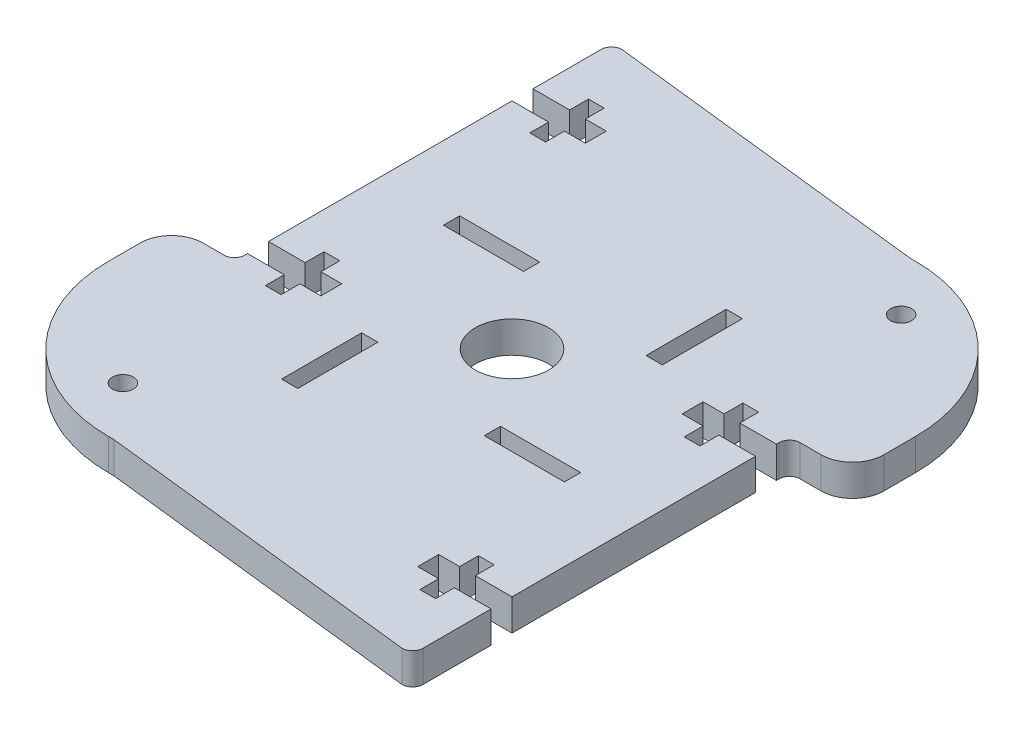
SolidWorks part; units mm, degrees
material "Acrílico (médio-alto impacto)"
ref_plane "Plano frontal" through (0, 0, 0) normal (0, 0, 1) x (1, 0, 0)
ref_plane "Plano superior" through (0, 0, 0) normal (0, 1, 0) x (1, 0, 0)
ref_plane "Plano direito" through (0, 0, 0) normal (1, 0, 0) x (0, 0, -1)
sketch "Esboço1" plane through (0, 0, 0) normal (0, 1, 0) x (1, 0, 0)
  line L1 (-26.5, -30) -> (26.5, -30)
  line L2 (-26.5, -30) -> (-26.5, 30)
  line L3 (-26.5, 30) -> (26.5, 30)
  line L4 (26.5, -30) -> (26.5, 30)
  line L5 (-26.5, -30) -> (26.5, 30) construction
  line L6 (-26.5, 30) -> (26.5, -30) construction
  point P0 (0, 0)
  dimension "D1" = 53
  dimension "D2" = 60
extrude "Ressalto-extrusão1" add sketch "Esboço1" along normal blind 3
sketch "Esboço4" plane through (0, 3, 0) normal (0, 1, 0) x (-1, 0, 0)
  line L0 (-11.5, -26.5) -> (11.5, -26.5) construction
  line L2 (-26.5, 30) -> (-26.5, -30) construction
  line B0 (-6.95, -13.5) -> (-8.5, -13.5)
  line B1 (-6.95, -13.5) -> (-6.95, -5.85)
  line B2 (-6.95, -5.85) -> (-8.5, -5.85)
  line B3 (-8.5, -13.5) -> (-8.5, -5.85)
  line B4 (-13.5, 6.95) -> (-13.5, 8.5)
  line B5 (-13.5, 6.95) -> (-5.85, 6.95)
  line B6 (-5.85, 6.95) -> (-5.85, 8.5)
  line B7 (-13.5, 8.5) -> (-5.85, 8.5)
  line B8 (6.95, 13.5) -> (8.5, 13.5)
  line B9 (6.95, 13.5) -> (6.95, 5.85)
  line B10 (6.95, 5.85) -> (8.5, 5.85)
  line B11 (8.5, 13.5) -> (8.5, 5.85)
  line B12 (13.5, -6.95) -> (13.5, -8.5)
  line B13 (13.5, -6.95) -> (5.85, -6.95)
  line B14 (5.85, -6.95) -> (5.85, -8.5)
  line B15 (13.5, -8.5) -> (5.85, -8.5)
  dimension "D1" = 18
  dimension "D2" = 13
sketch_block_instance "Bloco2-1"
sketch_block "Bloco2" parameters "D1"=7.65, "D2"=1.55
sketch_block_instance "Bloco2-5"
sketch_block_instance "Bloco2-14"
sketch_block_instance "Bloco2-15"
sketch_block_instance "Bloco2-16"
extrude "Corte-extrusão2" cut sketch "Esboço4" against normal blind 10
sketch "Esboço5" plane through (0, 3, 0) normal (0, 1, 0) x (1, 0, 0)
  circle A4 centre (-15.7426, -21.3995) radius 1
  circle A7 centre (15.7426, 21.3995) radius 1
  dimension "D4" = 2
extrude "Corte-extrusão3" cut sketch "Esboço5" against normal through all
sketch "Esboço7" plane through (0, 3, 0) normal (0, 1, 0) x (1, 0, 0)
  circle A0 centre (0, 0) radius 3.5
  dimension "D1" = 7
extrude "Corte-extrusão6" cut sketch "Esboço7" against normal through all
sketch "Esboço8" plane through (0, 3, 0) normal (0, 1, 0) x (1, 0, 0)
  line L0 (26.5, -30) -> (26.5, 30) construction
  line L1 (26.5, 6) -> (20.5, 6)
  line L2 (26.5, 6) -> (26.5, -30)
  line L3 (26.5, -30) -> (20.5, -30)
  line L4 (20.5, 6) -> (20.5, -30)
  line L5 (-26.5, -30) -> (26.5, -30) construction
  line L6 (-26.5, -6) -> (-20.5, -6)
  line L8 (-26.5, -6) -> (-26.5, 30)
  line L9 (-26.5, 30) -> (-20.5, 30)
  line L10 (-20.5, -6) -> (-20.5, 30)
  dimension "D1" = 6
  dimension "D2" = 36
  dimension "D3" = 2
extrude "Corte-extrusão7" cut sketch "Esboço8" against normal through all
fillet "Filete2" radius 3 2 edges at (-26.5, 1.5, 6) (26.5, 1.5, -6)
fillet "Filete3" radius 1 4 edges at (-20.5, 1.5, -30) (20.5, 1.5, 30) (-20.5, 1.5, 6) (20.5, 1.5, -6)
sketch "Esboço9" plane through (0, 3, 0) normal (0, 1, 0) x (1, 0, 0)
  line L0 (-20.5, -5) -> (-20.5, 29) construction
  line L1 (26.5, 30) -> (-19.5, 30) construction
  line B0 (-13.5, 20.5) -> (-15.5, 20.5)
  line B1 (-13.5, 20.5) -> (-13.5, 22.5)
  line B2 (-20.5, 20.5) -> (-20.5, 22.5)
  line B3 (-13.5, 22.5) -> (-15.5, 22.5)
  line B4 (-15.5, 18.7) -> (-15.5, 20.5)
  line B5 (-15.5, 18.7) -> (-17, 18.7)
  line B6 (-17, 18.7) -> (-17, 20.5)
  line B7 (-15.5, 24.3) -> (-17, 24.3)
  line B8 (-17, 22.5) -> (-20.5, 22.5)
  line B9 (-15.5, 22.5) -> (-15.5, 24.3)
  line B10 (-17, 22.5) -> (-17, 24.3)
  line B11 (-17, 20.5) -> (-20.5, 20.5)
  line B12 (-13.5, -4.7435) -> (-15.5, -4.7435)
  line B13 (-13.5, -4.7435) -> (-13.5, -2.7435)
  line B14 (-20.5, -4.7435) -> (-20.5, -2.7435)
  line B15 (-13.5, -2.7435) -> (-15.5, -2.7435)
  line B16 (-15.5, -6.5435) -> (-15.5, -4.7435)
  line B17 (-15.5, -6.5435) -> (-17, -6.5435)
  line B18 (-17, -6.5435) -> (-17, -4.7435)
  line B19 (-15.5, -0.9435) -> (-17, -0.9435)
  line B20 (-17, -2.7435) -> (-20.5, -2.7435)
  line B21 (-15.5, -2.7435) -> (-15.5, -0.9435)
  line B22 (-17, -2.7435) -> (-17, -0.9435)
  line B23 (-17, -4.7435) -> (-20.5, -4.7435)
  line B24 (13.5, -20.5) -> (15.5, -20.5)
  line B25 (13.5, -20.5) -> (13.5, -22.5)
  line B26 (20.5, -20.5) -> (20.5, -22.5)
  line B27 (13.5, -22.5) -> (15.5, -22.5)
  line B28 (15.5, -18.7) -> (15.5, -20.5)
  line B29 (15.5, -18.7) -> (17, -18.7)
  line B30 (17, -18.7) -> (17, -20.5)
  line B31 (15.5, -24.3) -> (17, -24.3)
  line B32 (17, -22.5) -> (20.5, -22.5)
  line B33 (15.5, -22.5) -> (15.5, -24.3)
  line B34 (17, -22.5) -> (17, -24.3)
  line B35 (17, -20.5) -> (20.5, -20.5)
  line B36 (13.5, 4.7435) -> (15.5, 4.7435)
  line B37 (13.5, 4.7435) -> (13.5, 2.7435)
  line B38 (20.5, 4.7435) -> (20.5, 2.7435)
  line B39 (13.5, 2.7435) -> (15.5, 2.7435)
  line B40 (15.5, 6.5435) -> (15.5, 4.7435)
  line B41 (15.5, 6.5435) -> (17, 6.5435)
  line B42 (17, 6.5435) -> (17, 4.7435)
  line B43 (15.5, 0.9435) -> (17, 0.9435)
  line B44 (17, 2.7435) -> (20.5, 2.7435)
  line B45 (15.5, 2.7435) -> (15.5, 0.9435)
  line B46 (17, 2.7435) -> (17, 0.9435)
  line B47 (17, 4.7435) -> (20.5, 4.7435)
  dimension "D1" = 8.5
  dimension "D2" = 25.2435
  dimension "D3" = 2
sketch_block_instance "encaixe_parafuso_acrilico-6"
sketch_block "encaixe_parafuso_acrilico" parameters "D1"=7, "D2"=2, "D3"=5, "D4"=1.5, "D5"=3.5, "D6"=1.5
sketch_block_instance "encaixe_parafuso_acrilico-7"
sketch_block_instance "encaixe_parafuso_acrilico-16"
sketch_block_instance "encaixe_parafuso_acrilico-17"
extrude "Corte-extrusão8" cut sketch "Esboço9" against normal through all
sketch "Esboço10" plane through (0, 3, 0) normal (0, 1, 0) x (1, 0, 0)
  line L0 (26.5, 11.5) -> (26.5, 12)
  line L1 (26.5, 9) -> (26.5, 30) construction
  line L2 (12, 26.5) -> (11.5, 26.5)
  line L3 (11.5, 26.5) -> (-19.5, 30)
  line L4 (-19.5, 30) -> (-19.5, 39.9976)
  line L5 (-19.5, 39.9976) -> (32.5343, 39.9976)
  line L6 (32.5343, 39.9976) -> (32.5343, 11.5)
  line L7 (32.5343, 11.5) -> (26.5, 11.5)
  line L8 (-26.5, -11.5) -> (-26.5, -12)
  line L9 (-12, -26.5) -> (-11.5, -26.5)
  line L10 (-11.5, -26.5) -> (19.5, -30)
  line L11 (19.5, -30) -> (19.5, -39.9976)
  line L12 (19.5, -39.9976) -> (-32.5343, -39.9976)
  line L13 (-32.5343, -39.9976) -> (-32.5343, -11.5)
  line L14 (-32.5343, -11.5) -> (-26.5, -11.5)
  arc A0 (26.5, 12) -> (12, 26.5) centre (12, 12) ccw
  arc A1 (-26.5, -12) -> (-12, -26.5) centre (-12, -12) ccw
  point P11 (26.5, 26.5)
  dimension "D1" = 14.5
  dimension "D2" = 2
extrude "Corte-extrusão9" cut sketch "Esboço10" against normal through all
sketch "Esboço11" plane through (0, 3, 0) normal (0, 1, 0) x (1, 0, 0)
  line L0 (20.5, 4.7435) -> (17, 4.7435)
  line L1 (17, 4.7435) -> (17, 6.5435)
  line L2 (17, 6.5435) -> (15.5, 6.5435)
  line L3 (15.5, 6.5435) -> (15.5, 4.7435)
  line L4 (15.5, 4.7435) -> (13.5, 4.7435)
  line L5 (13.5, 4.7435) -> (13.5, 2.7435)
  line L6 (13.5, 2.7435) -> (15.5, 2.7435)
  line L7 (15.5, 2.7435) -> (15.5, 0.9435)
  line L8 (15.5, 0.9435) -> (17, 0.9435)
  line L9 (17, 0.9435) -> (17, 2.7435)
  line L10 (17, 2.7435) -> (20.5, 2.7435)
  line L11 (20.5, 2.7435) -> (20.5, 4.7435)
